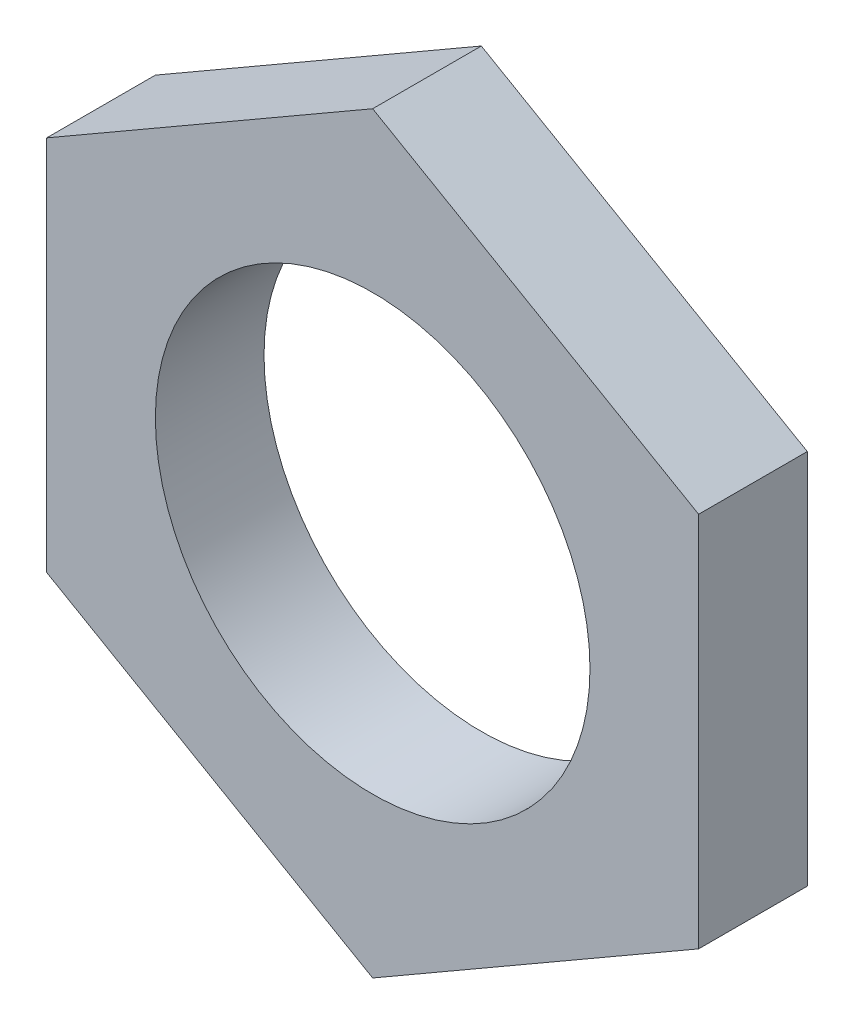
SolidWorks part; units mm, degrees
ref_plane "Спереди" through (0, 0, 0) normal (0, 0, 1) x (1, 0, 0)
ref_plane "Сверху" through (0, 0, 0) normal (0, 1, 0) x (1, 0, 0)
ref_plane "Справа" through (0, 0, 0) normal (1, 0, 0) x (0, 0, -1)
sketch "Эскиз1" plane through (0, 0, 0) normal (0, 0, 1) x (1, 0, 0)
  line L0 (0, 0) -> (0, 6.9282) construction
  line L1 (0, 6.9282) -> (-6, 3.4641)
  line L2 (-6, 3.4641) -> (-6, -3.4641)
  line L3 (-6, -3.4641) -> (0, -6.9282)
  line L4 (0, -6.9282) -> (6, -3.4641)
  line L5 (6, -3.4641) -> (6, 3.4641)
  line L6 (6, 3.4641) -> (0, 6.9282)
  circle A0 centre (0, 0) radius 6 construction
  circle A1 centre (0, 0) radius 4
  dimension "D1" = 8
  dimension "D2" = 12
extrude "Бобышка-Вытянуть1" add sketch "Эскиз1" along normal blind 2
